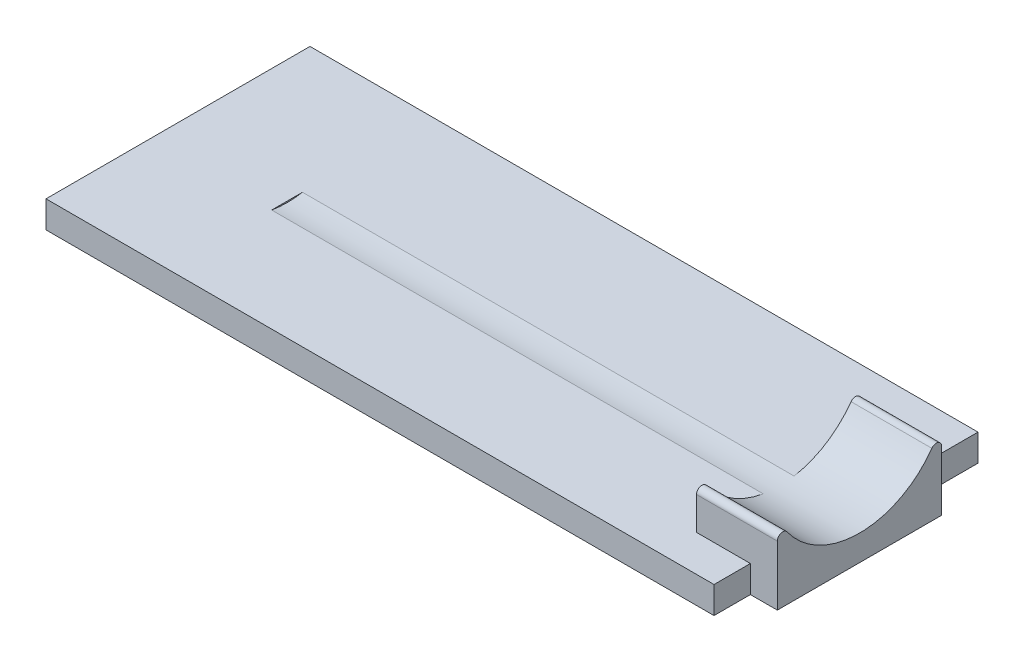
SolidWorks part; units mm, degrees
ref_plane "Front Plane" through (0, 0, 0) normal (0, 0, 1) x (1, 0, 0)
ref_plane "Top Plane" through (0, 0, 0) normal (0, 1, 0) x (1, 0, 0)
ref_plane "Right Plane" through (0, 0, 0) normal (1, 0, 0) x (0, 0, -1)
sketch "Sketch1" plane through (0, 0, 0) normal (0, 1, 0) x (1, 0, 0)
  line L1 (0, 0) -> (-24.8, 0)
  line L2 (0, 0) -> (0, 9.8)
  line L3 (0, 9.8) -> (-24.8, 9.8)
  line L4 (-24.8, 0) -> (-24.8, 9.8)
  dimension "D1" = 24.8
  dimension "D2" = 9.8
extrude "Boss-Extrude1" add sketch "Sketch1" along normal blind 1
sketch "Sketch2" plane through (0, 1, 0) normal (0, 1, 0) x (1, 0, 0)
  line L0 (-2.2883, 9.8) -> (-2.2883, 8.8) construction
  line L1 (0, 9.8) -> (-24.8, 9.8) construction
  line L2 (1, 1.35) -> (-2, 1.35)
  line L3 (-2, 1.35) -> (-2, 7.45)
  line L4 (-2, 7.45) -> (1, 7.45)
  line L5 (1, 7.45) -> (1, 1.35)
  line L7 (0, 0) -> (0, 1.35) construction
  line L8 (-2.2883, 8.8) -> (0, 8.8) construction
  line L9 (0, 0) -> (0, 9.8) construction
  line L10 (0, 8.8) -> (0, 7.45) construction
  dimension "D1" = 1
  dimension "D2" = 6.1
  dimension "D3" = 3
  dimension "D4" = 1
extrude "Boss-Extrude2" add sketch "Sketch2" along normal blind 3.25
sketch "Sketch4" plane through (0, 1, 0) normal (0, -1, 0) x (1, 0, 0)
  line L1 (0, -1.35) -> (1, -1.35)
  line L2 (0, -1.35) -> (0, -7.45)
  line L3 (0, -7.45) -> (1, -7.45)
  line L4 (1, -1.35) -> (1, -7.45)
extrude "Boss-Extrude3" add sketch "Sketch4" along normal up to surface (1 mm away) up to face at (-12.4, 0, -4.9)
sketch "Sketch3" plane through (1, 0, 0) normal (1, 0, 0) x (0, 0, -1)
  line L0 (1.1, 4.25) -> (7.7, 4.25) construction
  line L1 (1.35, 4.25) -> (7.45, 4.25) construction
  circle A0 centre (4.4, 4.25) radius 3.3
  point P2 (4.35, 4.25)
  dimension "D1" = 6.6
extrude "Cut-Extrude1" cut sketch "Sketch3" against normal blind 21.25
fillet "Fillet1" radius 0.2 2 edges at (-0.5, 2.99, -7.45) (-0.5, 2.99, -1.35)
